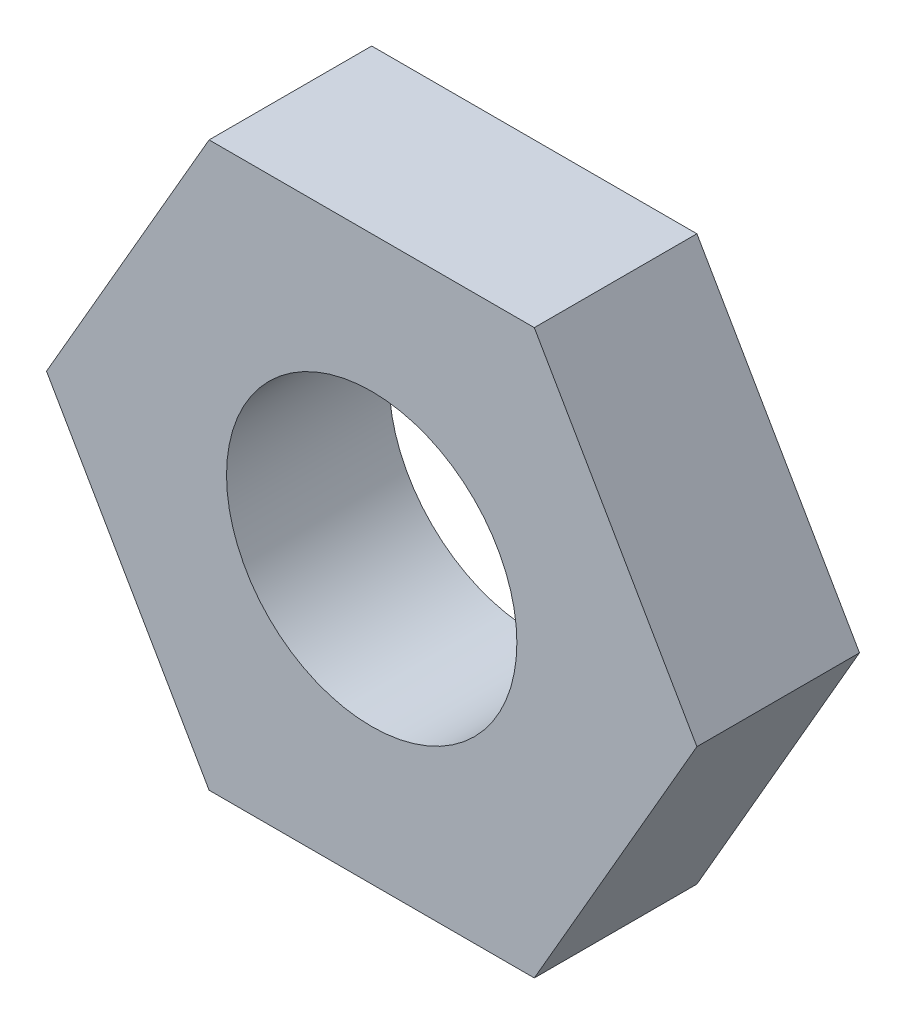
SolidWorks part; units mm, degrees
ref_plane "Front Plane" through (0, 0, 0) normal (0, 0, 1) x (1, 0, 0)
ref_plane "Top Plane" through (0, 0, 0) normal (0, 1, 0) x (1, 0, 0)
ref_plane "Right Plane" through (0, 0, 0) normal (1, 0, 0) x (0, 0, -1)
sketch "Sketch2" plane through (0, 0, 0) normal (0, 0, 1) x (1, 0, 0)
  line L1 (-7.112, 0) -> (-3.556, -6.1592)
  line L2 (-3.556, -6.1592) -> (3.556, -6.1592)
  line L3 (3.556, -6.1592) -> (7.112, 0)
  line L4 (7.112, 0) -> (3.556, 6.1592)
  line L5 (3.556, 6.1592) -> (-3.556, 6.1592)
  line L6 (-3.556, 6.1592) -> (-7.112, 0)
  circle A0 centre (0, 0) radius 3.175
  circle A1 centre (0, 0) radius 6.1592 construction
  dimension "D1" = 6.35
  dimension "D2" = 14.224
extrude "Boss-Extrude1" add sketch "Sketch2" along normal blind 3.556
